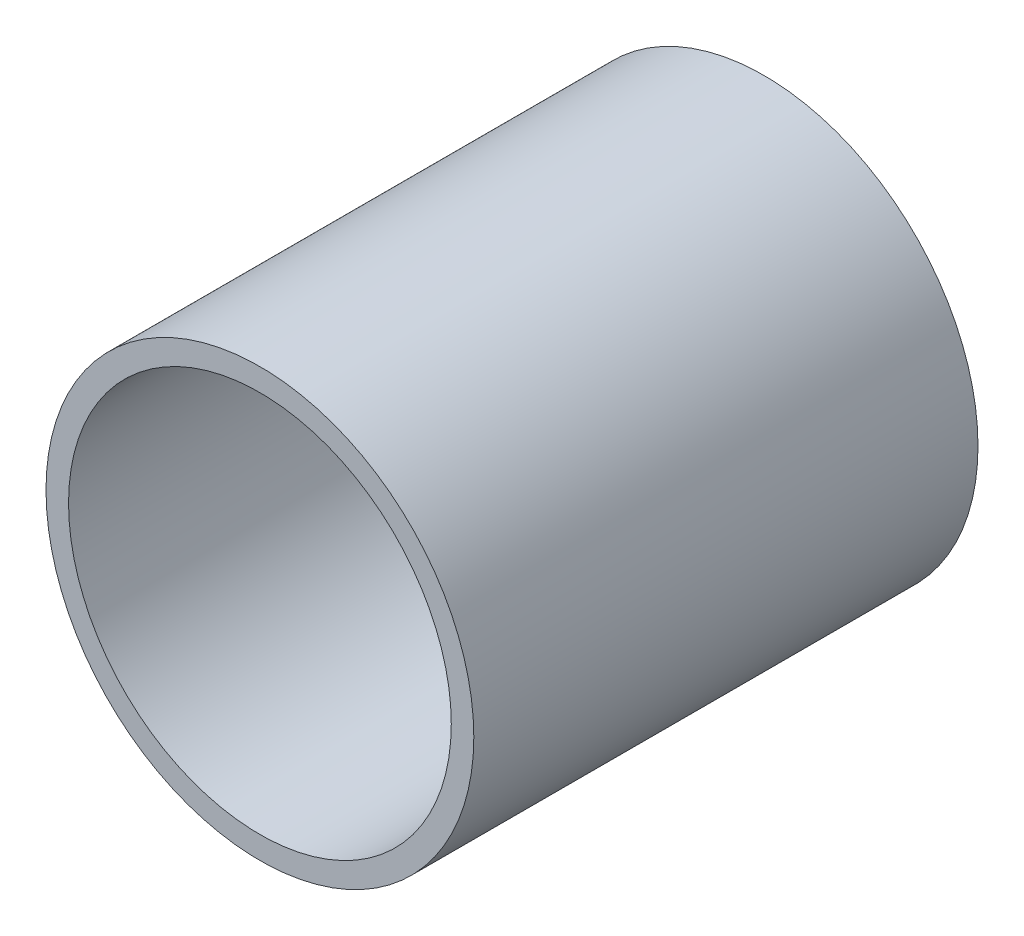
SolidWorks part; units mm, degrees
ref_plane "Front Plane" through (0, 0, 0) normal (0, 0, 1) x (1, 0, 0)
ref_plane "Top Plane" through (0, 0, 0) normal (0, 1, 0) x (1, 0, 0)
ref_plane "Right Plane" through (0, 0, 0) normal (1, 0, 0) x (0, 0, -1)
sketch "Sketch1" plane through (0, 0, 0) normal (0, 0, 1) x (1, 0, 0)
  circle A0 centre (0, 0) radius 57.15
  dimension "Pipe OD" = 114.3
extrude "Extrude-Thin1" add sketch "Sketch1" along normal mid plane 134.7 thin thin type one direction reverse wall 6.0198
